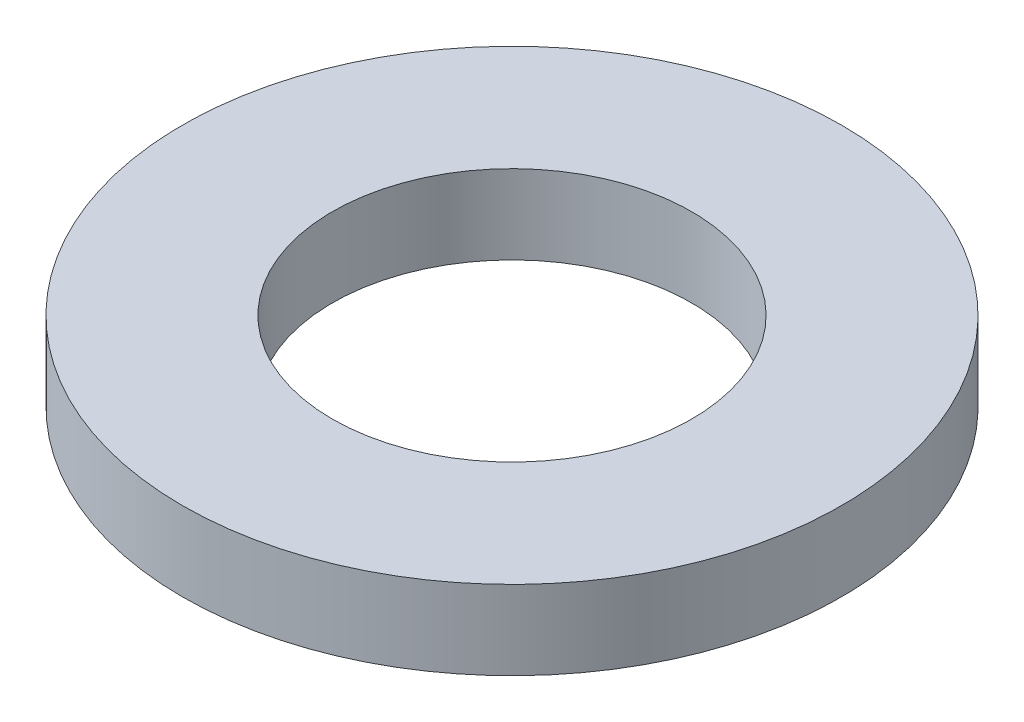
SolidWorks part; units mm, degrees
ref_plane "Front Plane" through (0, 0, 0) normal (0, 0, 1) x (1, 0, 0)
ref_plane "Top Plane" through (0, 0, 0) normal (0, 1, 0) x (1, 0, 0)
ref_plane "Right Plane" through (0, 0, 0) normal (1, 0, 0) x (0, 0, -1)
other "Bounding Box"
ref_plane "Default Plane" through (13.8565, 3.175, 6.7999) normal (0, -1, 0) x (-1, 0, 0)
sketch "Sketch1" plane through (0, 0, 0) normal (0, 1, 0) x (1, 0, 0)
  circle A0 centre (0, 0) radius 6.35
  circle A1 centre (0, 0) radius 11.6459
  dimension "D1" = 12.7
  dimension "D2" = 23.2918
extrude "Boss-Extrude1" add sketch "Sketch1" along normal mid plane 2.794
